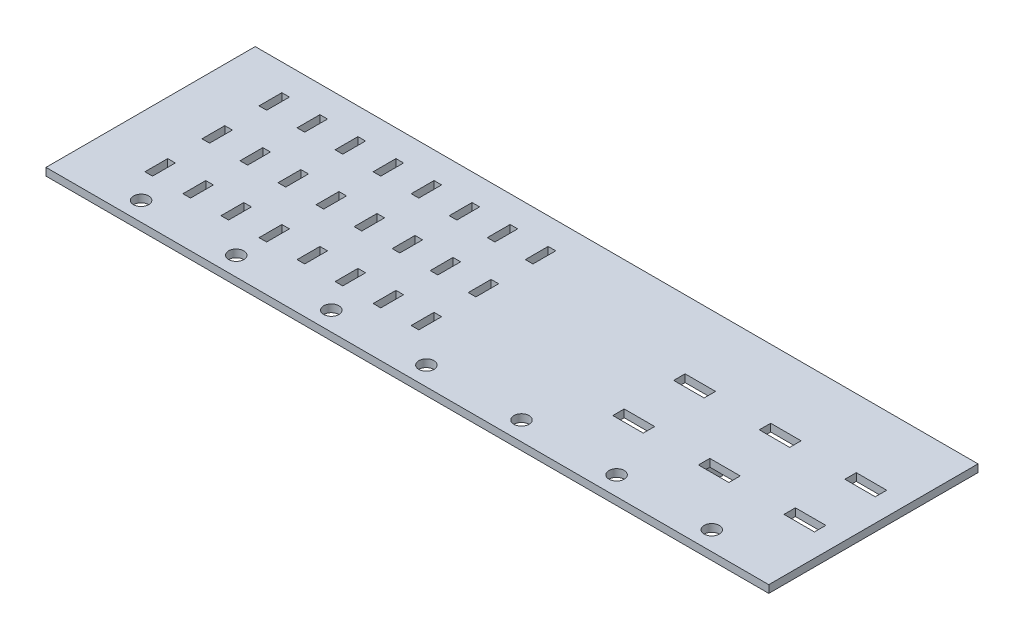
SolidWorks part; units mm, degrees
ref_plane "Front Plane" through (0, 0, 0) normal (0, 0, 1) x (1, 0, 0)
ref_plane "Top Plane" through (0, 0, 0) normal (0, 1, 0) x (1, 0, 0)
ref_plane "Right Plane" through (0, 0, 0) normal (1, 0, 0) x (0, 0, -1)
sketch "Sketch1" plane through (0, 0, 0) normal (0, 1, 0) x (1, 0, 0)
  line L0 (75, 0) -> (75, 22.5) construction
  line L2 (-20, 50) -> (170, 50)
  line L3 (-20, 50) -> (-20, -5)
  line L4 (-20, -5) -> (170, -5)
  line L5 (170, 50) -> (170, -5)
  line L6 (-20, 50) -> (170, -5) construction
  line L7 (-20, -5) -> (170, 50) construction
  circle A0 centre (0, 0) radius 2
  circle A1 centre (25, 0) radius 2
  circle A2 centre (50, 0) radius 2
  circle A3 centre (75, 0) radius 2
  circle A4 centre (100, 0) radius 2
  circle A5 centre (125, 0) radius 2
  circle A6 centre (150, 0) radius 2
  dimension "D1" = 4
  dimension "D3" = 25
  dimension "D4" = 50
  dimension "D5" = 5
  dimension "D6" = 190
  dimension "D2" = 7
extrude "Boss-Extrude1" add sketch "Sketch1" along normal blind 2
sketch "Sketch2" plane through (0, 0, 0) normal (0, -1, 0) x (1, 0, 0)
  line L0 (-20, -22.5) -> (170, -22.5) construction
  line L1 (-20, -50) -> (-20, 5) construction
  line L2 (170, 5) -> (170, -50) construction
  line L4 (125, 0) -> (125, -22.5) construction
  line L12 (120, -17.5) -> (130, -17.5)
  line L13 (120, -17.5) -> (120, -27.5)
  line L14 (120, -27.5) -> (130, -27.5)
  line L15 (130, -17.5) -> (130, -27.5)
  line L16 (120, -17.5) -> (130, -27.5) construction
  line L17 (120, -27.5) -> (130, -17.5) construction
  dimension "D3" = 10
  dimension "D4" = 10
extrude "Boss-Extrude2" add sketch "Sketch2" along normal blind 7.1
pattern_linear "LPattern1" count 2 spacing 22.5 along (0, 0, -1) of "Boss-Extrude2"
sketch "Sketch3" plane through (0, 2, 0) normal (0, 1, 0) x (1, 0, 0)
  line L0 (-20, 22.5) -> (170, 22.5) construction
  line L1 (-20, 50) -> (-20, -5) construction
  line L2 (170, -5) -> (170, 50) construction
  line L3 (160, 30.5) -> (160, 14.5) construction
  line L5 (164, 32) -> (156, 32)
  line L6 (164, 32) -> (164, 29)
  line L7 (164, 29) -> (156, 29)
  line L8 (156, 32) -> (156, 29)
  line L9 (164, 32) -> (156, 29) construction
  line L10 (164, 29) -> (156, 32) construction
  line L11 (164, 16) -> (156, 16)
  line L12 (164, 16) -> (164, 13)
  line L13 (164, 13) -> (156, 13)
  line L14 (156, 16) -> (156, 13)
  line L15 (164, 16) -> (156, 13) construction
  line L16 (164, 13) -> (156, 16) construction
  point P9 (160, 22.5)
  dimension "D1" = 8
  dimension "D2" = 3
  dimension "D3" = 16
  dimension "D4" = 10
extrude "Cut-Extrude1" cut sketch "Sketch3" against normal blind 7.1
pattern_linear "LPattern2" count 3 spacing 22.5 along (-1, 0, 0) of "Cut-Extrude1"
sketch "Sketch4" plane through (0, 2, 0) normal (0, 1, 0) x (1, 0, 0)
  line L0 (0, -5) -> (0, 50) construction
  line L1 (-20, -5) -> (170, -5) construction
  line L2 (170, 50) -> (-20, 50) construction
  line L3 (-5, 10) -> (5, 10) construction
  line L4 (-20, 50) -> (-20, -5) construction
  line L5 (-4, 13) -> (-6, 13)
  line L6 (-4, 13) -> (-4, 7)
  line L7 (-4, 7) -> (-6, 7)
  line L8 (-6, 13) -> (-6, 7)
  line L9 (-4, 13) -> (-6, 7) construction
  line L10 (-4, 7) -> (-6, 13) construction
  line L11 (4, 13) -> (6, 13)
  line L12 (4, 13) -> (4, 7)
  line L13 (4, 7) -> (6, 7)
  line L14 (6, 13) -> (6, 7)
  line L15 (4, 13) -> (6, 7) construction
  line L16 (4, 7) -> (6, 13) construction
  point P9 (0, 10)
  dimension "D1" = 10
  dimension "D2" = 2
  dimension "D3" = 2
  dimension "D4" = 6
  dimension "D5" = 6
  dimension "D6" = 15
  dimension "D7" = 20
extrude "Cut-Extrude2" cut sketch "Sketch4" against normal blind 7.1
pattern_linear "LPattern3" count 3 spacing 15 along (0, 0, -1) of "Cut-Extrude2"
pattern_linear "LPattern4" count 4 spacing 20 along (1, 0, 0) of "LPattern3", "Cut-Extrude2"
sketch "Sketch5" plane through (0, 0, 0) normal (0, -1, 0) x (1, 0, 0)
  line L0 (-20, -40) -> (-10, -40)
  line L1 (-20, -50) -> (-20, 5) construction
  line L2 (-10, -40) -> (-10, -50)
  line L3 (120, -50) -> (-20, -50) construction
  line L4 (-10, -50) -> (-20, -50)
  line L5 (-20, -50) -> (-20, -40)
  line L6 (-20, -15) -> (-10, -15)
  line L7 (-10, -15) -> (-10, -25)
  line L8 (-10, -25) -> (-20, -25)
  line L9 (-20, -25) -> (-20, -15)
  dimension "D1" = 10
  dimension "D2" = 10
  dimension "D3" = 10
  dimension "D4" = 10
  dimension "D5" = 25
extrude "Boss-Extrude3" add sketch "Sketch5" along normal blind 7.1
